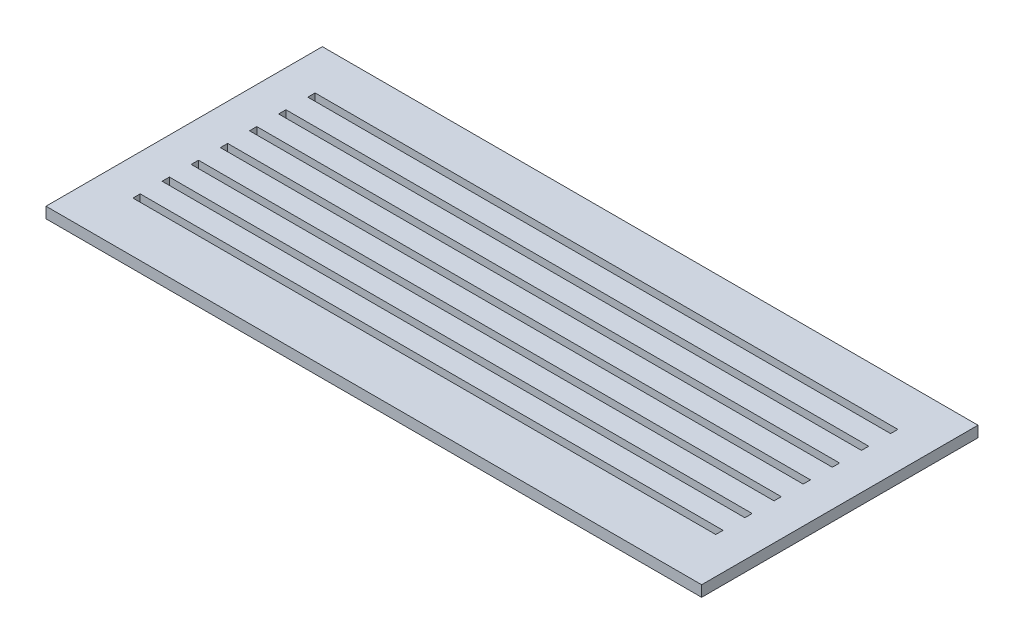
SolidWorks part; units mm, degrees
ref_plane "Front Plane" through (0, 0, 0) normal (0, 0, 1) x (1, 0, 0)
ref_plane "Top Plane" through (0, 0, 0) normal (0, 1, 0) x (1, 0, 0)
ref_plane "Right Plane" through (0, 0, 0) normal (1, 0, 0) x (0, 0, -1)
sketch "Sketch1" plane through (0, 0, 0) normal (0, 1, 0) x (1, 0, 0)
  line L0 (-85.567, 25.3965) -> (74.433, 25.3965)
  line L1 (-95.567, 45.3965) -> (84.433, 45.3965)
  line L2 (-95.567, 45.3965) -> (-95.567, -30.4735)
  line L3 (-95.567, -30.4735) -> (84.433, -30.4735)
  line L4 (84.433, 45.3965) -> (84.433, -30.4735)
  line L5 (-85.567, 33.3965) -> (74.433, 33.3965)
  line L6 (-85.567, 33.3965) -> (-85.567, 31.3965)
  line L7 (-85.567, 31.3965) -> (74.433, 31.3965)
  line L8 (74.433, 33.3965) -> (74.433, 31.3965)
  line L9 (-85.567, 25.3965) -> (-85.567, 23.3965)
  line L10 (-85.567, 23.3965) -> (74.433, 23.3965)
  line L11 (74.433, 25.3965) -> (74.433, 23.3965)
  line L12 (-85.567, 17.3965) -> (74.433, 17.3965)
  line L13 (-85.567, 17.3965) -> (-85.567, 15.3965)
  line L14 (-85.567, 15.3965) -> (74.433, 15.3965)
  line L15 (74.433, 17.3965) -> (74.433, 15.3965)
  line L16 (-85.567, 9.3965) -> (74.433, 9.3965)
  line L17 (-85.567, 9.3965) -> (-85.567, 7.3965)
  line L18 (-85.567, 7.3965) -> (74.433, 7.3965)
  line L19 (74.433, 9.3965) -> (74.433, 7.3965)
  line L20 (-85.567, 1.3965) -> (74.433, 1.3965)
  line L21 (-85.567, 1.3965) -> (-85.567, -0.6035)
  line L22 (-85.567, -0.6035) -> (74.433, -0.6035)
  line L23 (74.433, 1.3965) -> (74.433, -0.6035)
  line L24 (-85.567, -6.6035) -> (74.433, -6.6035)
  line L25 (-85.567, -6.6035) -> (-85.567, -8.6035)
  line L26 (-85.567, -8.6035) -> (74.433, -8.6035)
  line L27 (74.433, -6.6035) -> (74.433, -8.6035)
  line L28 (-85.567, -14.6035) -> (74.433, -14.6035)
  line L29 (-85.567, -14.6035) -> (-85.567, -16.6035)
  line L30 (-85.567, -16.6035) -> (74.433, -16.6035)
  line L31 (74.433, -14.6035) -> (74.433, -16.6035)
  line L90 (84.433, 7.4615) -> (104.4321, 7.4615) construction
  dimension "D1" = 180
  dimension "D2" = 75.87
  dimension "D3" = 160
  dimension "D4" = 2
  dimension "D5" = 10
  dimension "D6" = 12
  dimension "D7" = 7
extrude "Boss-Extrude1" add sketch "Sketch1" along normal blind 3
